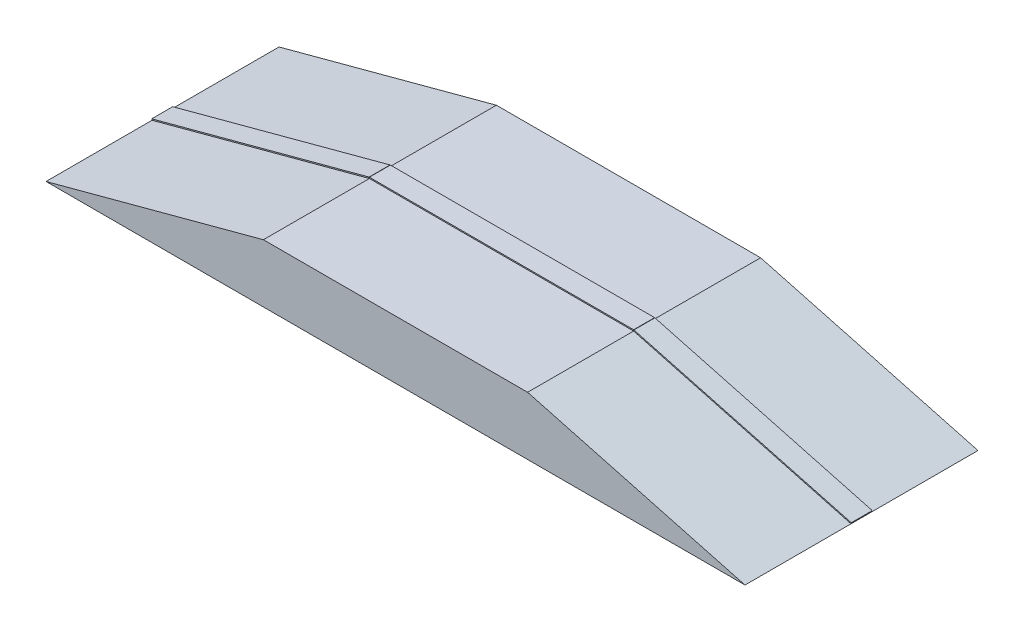
SolidWorks part; units mm, degrees
ref_plane "Front" through (0, 0, 0) normal (0, 0, 1) x (1, 0, 0)
ref_plane "Top" through (0, 0, 0) normal (0, 1, 0) x (1, 0, 0)
ref_plane "Right" through (0, 0, 0) normal (1, 0, 0) x (0, 0, -1)
sketch "草圖1" plane through (0, 0, 0) normal (0, 0, 1) x (1, 0, 0)
  line L0 (0, 0) -> (600, 0)
  line L1 (600, 0) -> (413.3975, 50)
  line L2 (413.3975, 50) -> (186.6025, 50)
  line L3 (186.6025, 50) -> (0, 0)
  dimension "D1" = 600
  dimension "D2" = 50
  dimension "D3" = 15
  dimension "D4" = 15
  dimension "D5" = 226.7949
extrude "填料-伸長1" add sketch "草圖1" along normal mid plane 200
sketch "草圖3" plane through (40.1924, 150, 0) normal (0.2588, 0.9659, 0) x (0.9659, -0.2588, 0)
  line L0 (579.5555, -100) -> (579.5555, 100) construction
  line L1 (579.5555, 9) -> (386.3703, 9)
  line L2 (579.5555, 9) -> (579.5555, -9)
  line L3 (579.5555, -9) -> (386.3703, -9)
  line L4 (386.3703, 9) -> (386.3703, -9)
  line L5 (386.3703, -100) -> (386.3703, 100) construction
  line L6 (579.5555, -100) -> (386.3703, -100) construction
  dimension "D1" = 18
  dimension "D2" = 91
extrude "填料-伸長2" add sketch "草圖3" along normal blind 1 separate body
sketch "草圖4" plane through (0, 50, 0) normal (0, 1, 0) x (1, 0, 0)
  line L0 (186.6025, -100) -> (186.6025, 100) construction
  line L1 (413.3975, 9) -> (186.6025, 9)
  line L2 (413.3975, 9) -> (413.3975, -9)
  line L3 (413.3975, -9) -> (186.6025, -9)
  line L4 (186.6025, 9) -> (186.6025, -9)
extrude "填料-伸長3" add sketch "草圖4" along normal blind 1 separate body
sketch "草圖5" plane through (0, 0, 0) normal (-0.2588, 0.9659, 0) x (0.9659, 0.2588, 0)
  line L0 (0, -100) -> (0, 100) construction
  line L1 (193.1852, 9) -> (0, 9)
  line L2 (193.1852, 9) -> (193.1852, -9)
  line L3 (193.1852, -9) -> (0, -9)
  line L4 (0, 9) -> (0, -9)
  line L5 (193.1852, 9) -> (193.1852, -9) construction
  line L6 (193.1852, -100) -> (193.1852, 100) construction
  dimension "D1" = 18
extrude "填料-伸長4" add sketch "草圖5" along normal blind 1 separate body
